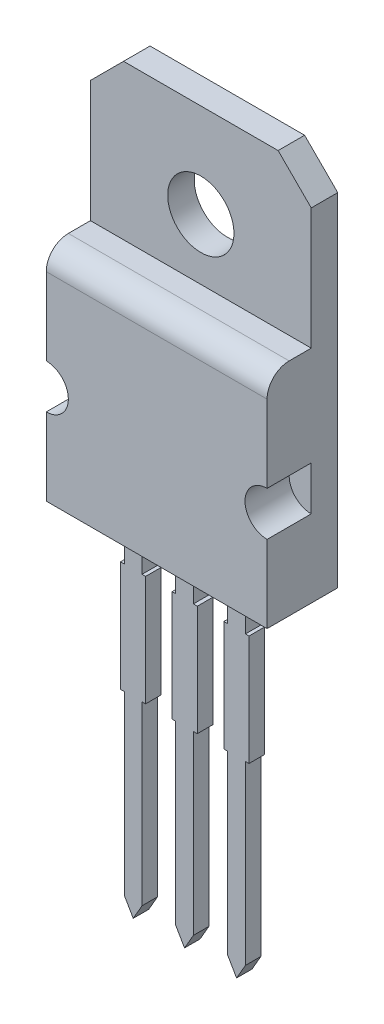
SolidWorks part; units mm, degrees
ref_plane "Front Plane" through (0, 0, 0) normal (0, 0, 1) x (1, 0, 0)
ref_plane "Top Plane" through (0, 0, 0) normal (0, 1, 0) x (1, 0, 0)
ref_plane "Right Plane" through (0, 0, 0) normal (1, 0, 0) x (0, 0, -1)
sketch "Sketch1" plane through (0, 0, 0) normal (0, 0, 1) x (1, 0, 0)
  line L1 (0, 0) -> (20.32, 0)
  line L2 (0, 0) -> (0, -50.8)
  line L5 (0, -381) -> (10.16, -398.5976)
  line L6 (10.16, -398.5976) -> (20.32, -381)
  line L7 (20.32, 0) -> (20.32, -50.8)
  line L8 (20.32, -177.8) -> (24.4325, -177.8)
  line L9 (-4.5235, -50.8) -> (0, -50.8)
  line L10 (-4.5235, -50.8) -> (-4.5235, -177.8)
  line L11 (-4.5235, -177.8) -> (0, -177.8)
  line L12 (24.4325, -50.8) -> (24.4325, -177.8)
  line L13 (20.32, -50.8) -> (24.4325, -50.8)
  line L14 (-59.847, -50.8) -> (-59.847, 0)
  line L15 (0, -177.8) -> (0, -381)
  line L16 (20.32, -177.8) -> (20.32, -381)
  line L18 (-59.847, -177.8) -> (-59.847, -381)
  line L19 (-39.527, -177.8) -> (-39.527, -381)
  line L20 (-59.847, -50.8) -> (-63.9595, -50.8)
  line L21 (-63.9595, -50.8) -> (-63.9595, -177.8)
  line L22 (-35.0035, -177.8) -> (-39.527, -177.8)
  line L23 (-35.0035, -50.8) -> (-35.0035, -177.8)
  line L24 (-35.0035, -50.8) -> (-39.527, -50.8)
  line L25 (-59.847, -177.8) -> (-63.9595, -177.8)
  line L26 (-49.687, -398.5976) -> (-59.847, -381)
  line L27 (-39.527, -381) -> (-49.687, -398.5976)
  line L29 (-59.847, 0) -> (-39.527, 0)
  line L32 (-118.872, -381) -> (-108.712, -398.5976)
  line L33 (-108.712, -398.5976) -> (-98.552, -381)
  line L34 (-98.552, -177.8) -> (-94.4395, -177.8)
  line L35 (-123.3955, -50.8) -> (-118.872, -50.8)
  line L36 (-123.3955, -50.8) -> (-123.3955, -177.8)
  line L37 (-123.3955, -177.8) -> (-118.872, -177.8)
  line L38 (-94.4395, -50.8) -> (-94.4395, -177.8)
  line L39 (-98.552, -50.8) -> (-94.4395, -50.8)
  line L40 (-118.872, -177.8) -> (-118.872, -381)
  line L41 (-98.552, -177.8) -> (-98.552, -381)
  line L42 (-39.527, 0) -> (-39.527, -50.8)
  line L43 (-118.872, -50.8) -> (-118.872, 0)
  line L44 (-118.872, 0) -> (-98.552, 0)
  line L45 (-98.552, 0) -> (-98.552, -50.8)
extrude "Boss-Extrude1" add sketch "Sketch1" along normal blind 17.78
sketch "Sketch2" plane through (0, 0, 0) normal (0, 0, 1) x (1, 0, 0)
  line L0 (-118.872, 0) -> (-175.7242, 0) construction
  line L1 (20.32, 0) -> (78.2758, 0) construction
  line L3 (-175.7242, 0) -> (78.2758, 0)
  line L4 (-175.7242, 0) -> (-175.7242, 254)
  line L5 (-175.7242, 254) -> (78.2758, 254)
  line L6 (78.2758, 0) -> (78.2758, 254)
  dimension "D1" = 254
  dimension "D2" = 254
extrude "Boss-Extrude2" add sketch "Sketch2" along normal blind 50.8
fillet "Fillet1" radius 25.4 1 edges at (-48.7242, 254, 50.8)
sketch "Sketch3" plane through (0, 0, 50.8) normal (0, 0, 1) x (1, 0, 0)
  line L0 (-175.7242, 114.3) -> (78.2758, 114.3) construction
  line L1 (-175.7242, 228.6) -> (-175.7242, 0) construction
  line L2 (78.2758, 0) -> (78.2758, 228.6) construction
  circle A0 centre (-175.7242, 114.3) radius 25.4
  circle A1 centre (78.2758, 114.3) radius 25.4
  dimension "D1" = 50.8
  dimension "D2" = 50.8
extrude "Cut-Extrude1" cut sketch "Sketch3" against normal blind 50.8
sketch "Sketch4" plane through (0, 0, 0) normal (0, 0, -1) x (-1, 0, 0)
  line L0 (-78.2758, 393.7) -> (-40.1758, 431.8)
  line L1 (-78.2758, 0) -> (175.7242, 0)
  line L2 (-78.2758, 0) -> (-78.2758, 393.7)
  line L3 (-40.1758, 431.8) -> (137.6242, 431.8)
  line L4 (175.7242, 0) -> (175.7242, 393.7)
  line L5 (137.6242, 431.8) -> (175.7242, 393.7)
  point P1 (175.7242, 431.8)
  point P2 (-78.2758, 431.8)
  dimension "D1" = 431.8
  dimension "D2" = 254
extrude "Boss-Extrude3" add sketch "Sketch4" along normal blind 30.48
sketch "Sketch5" plane through (0, 0, 0) normal (0, 0, 1) x (1, 0, 0)
  line L0 (-175.7242, 323.85) -> (78.2758, 323.85) construction
  line L1 (-175.7242, 254) -> (-175.7242, 393.7) construction
  line L2 (78.2758, 393.7) -> (78.2758, 254) construction
  circle A0 centre (-48.7242, 323.85) radius 38.1
  dimension "D1" = 76.2
extrude "Cut-Extrude2" cut sketch "Sketch5" against normal blind 30.48
